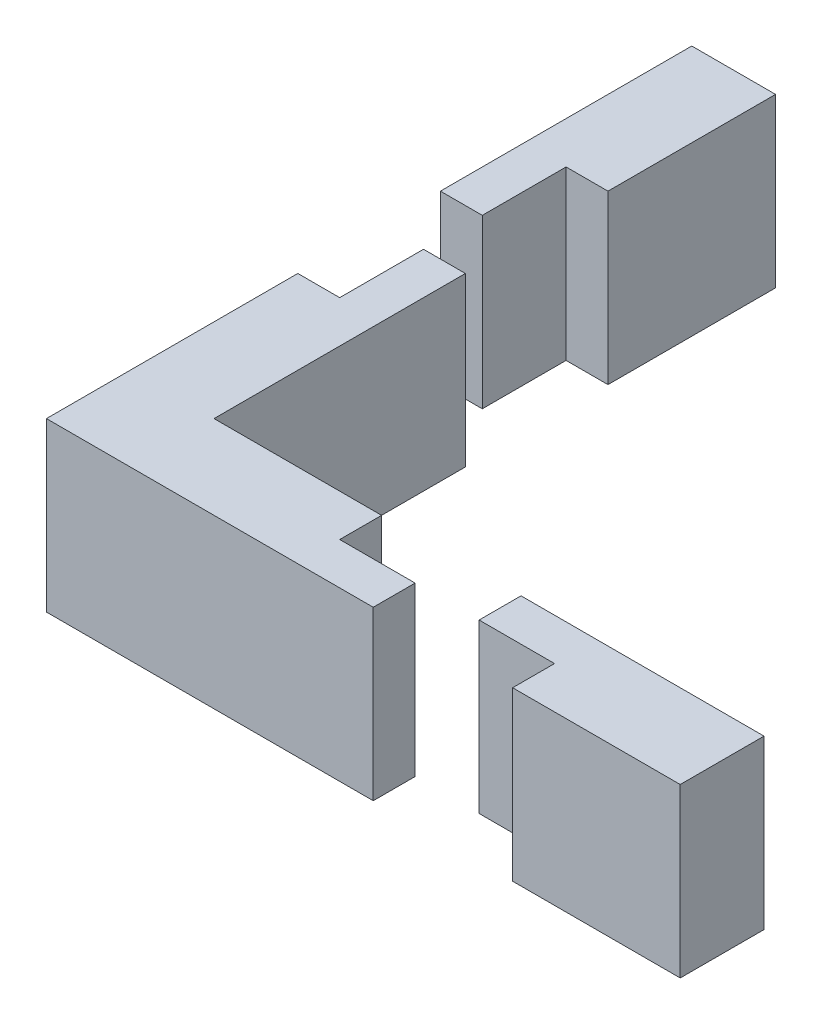
SolidWorks part; units mm, degrees
ref_plane "Front Plane" through (0, 0, 0) normal (0, 0, 1) x (1, 0, 0)
ref_plane "Top Plane" through (0, 0, 0) normal (0, 1, 0) x (1, 0, 0)
ref_plane "Right Plane" through (0, 0, 0) normal (1, 0, 0) x (0, 0, -1)
sketch "Sketch1" plane through (0, 0, 0) normal (0, 1, 0) x (1, 0, 0)
  line L1 (-2.5, 7.5) -> (2.5, 7.5)
  line L2 (-2.5, 7.5) -> (-2.5, -7.5)
  line L3 (-2.5, -7.5) -> (2.5, -7.5)
  line L4 (2.5, 7.5) -> (2.5, -7.5)
  line L5 (-2.5, 7.5) -> (2.5, -7.5) construction
  line L6 (-2.5, -7.5) -> (2.5, 7.5) construction
  line L7 (2.5, -7.5) -> (12.5, -7.5)
  line L8 (2.5, -7.5) -> (2.5, -2.5)
  line L9 (2.5, -2.5) -> (12.5, -2.5)
  line L10 (12.5, -7.5) -> (12.5, -2.5)
  line L11 (2.5, 7.5) -> (0, 7.5)
  line L12 (2.5, 7.5) -> (2.5, 12.5)
  line L13 (2.5, 12.5) -> (0, 12.5)
  line L14 (0, 7.5) -> (0, 12.5)
  line L15 (12.5, -7.5) -> (17, -7.5)
  line L16 (12.5, -7.5) -> (12.5, -5)
  line L17 (12.5, -5) -> (17, -5)
  line L18 (17, -7.5) -> (17, -5)
  line L19 (0, 16.0085) -> (-2.5, 16.0085)
  line L20 (0, 16.0085) -> (0, 21.0085)
  line L21 (0, 21.0085) -> (-2.5, 21.0085)
  line L22 (-2.5, 16.0085) -> (-2.5, 21.0085)
  line L23 (-2.5, 21.0085) -> (2.5, 21.0085)
  line L24 (-2.5, 21.0085) -> (-2.5, 31.0085)
  line L25 (-2.5, 31.0085) -> (2.5, 31.0085)
  line L26 (2.5, 21.0085) -> (2.5, 31.0085)
  line L27 (20.8194, -5) -> (25.3194, -5)
  line L28 (20.8194, -5) -> (20.8194, -2.5)
  line L29 (20.8194, -2.5) -> (25.3194, -2.5)
  line L30 (25.3194, -5) -> (25.3194, -2.5)
  line L31 (25.3194, -2.5) -> (35.3194, -2.5)
  line L32 (25.3194, -2.5) -> (25.3194, -7.5)
  line L33 (25.3194, -7.5) -> (35.3194, -7.5)
  line L34 (35.3194, -2.5) -> (35.3194, -7.5)
  point P0 (0, 0)
  dimension "D1" = 5
  dimension "D2" = 15
  dimension "D3" = 5
  dimension "D4" = 10
  dimension "D5" = 2.5
  dimension "D6" = 5
  dimension "D7" = 2.5
  dimension "D8" = 4.5
  dimension "D9" = 2.5
  dimension "D10" = 5
  dimension "D11" = 10
  dimension "D12" = 5
  dimension "D13" = 4.5
  dimension "D14" = 2.5
  dimension "D15" = 10
  dimension "D16" = 5
extrude "Boss-Extrude2" add sketch "Sketch1" along normal blind 10 contours L23 L26 L25 L24 L21 | L22 L19 L20 L21 | L14 L1 L12 L13 | L4 L1 L2 L3 | L7 L10 L9 L4 | L15 L18 L17 L10 | L27 L30 L29 L28 | L34 L31 L30 L32 L33
